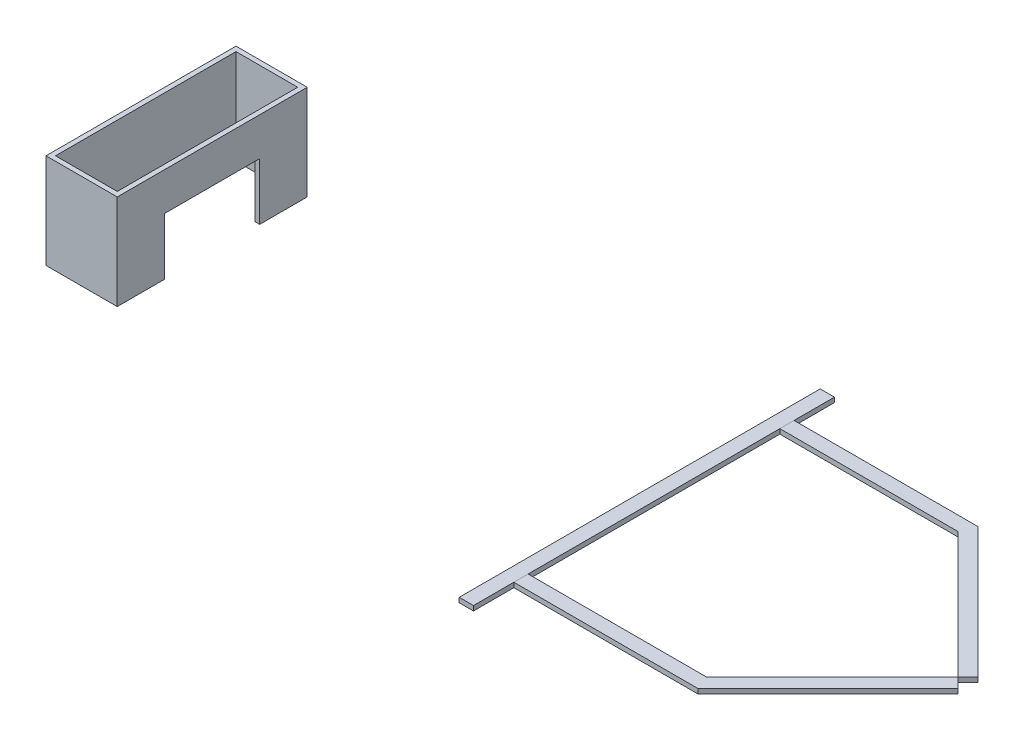
SolidWorks part; units mm, degrees
ref_plane "Front Plane" through (0, 0, 0) normal (0, 0, 1) x (1, 0, 0)
ref_plane "Top Plane" through (0, 0, 0) normal (0, 1, 0) x (1, 0, 0)
ref_plane "Right Plane" through (0, 0, 0) normal (1, 0, 0) x (0, 0, -1)
sketch "Sketch1" plane through (0, 0, 0) normal (0, 1, 0) x (1, 0, 0)
  line L6 (346.8244, -129.6488) -> (368.0376, -108.4356)
  line L16 (-292.9422, 135.3512) -> (81.8244, 135.3512)
  line L17 (81.8244, 135.3512) -> (346.8244, -129.6488)
  line L18 (-292.9422, 165.3512) -> (94.2508, 165.3512)
  line L19 (94.2508, 165.3512) -> (368.0376, -108.4356)
  line L20 (-292.9422, 165.3512) -> (-292.9422, 135.3512)
  line L21 (368.0376, -108.4356) -> (346.8244, -129.6488)
  line L22 (368.0376, -150.862) -> (346.8244, -129.6488)
  line L23 (-292.9422, -424.6488) -> (-292.9422, -394.6488)
  line L24 (94.2508, -424.6488) -> (368.0376, -150.862)
  line L25 (-292.9422, -424.6488) -> (94.2508, -424.6488)
  line L26 (81.8244, -394.6488) -> (346.8244, -129.6488)
  line L27 (-292.9422, -394.6488) -> (81.8244, -394.6488)
  point P1 (0, 0)
  point P2 (0, 0)
  dimension "D2" = 374.7666
  dimension "D3" = 374.7666
  dimension "D4" = 30
  dimension "D1" = 530
extrude "Boss-Extrude2" add sketch "Sketch1" along normal blind 10 contours L27 L23 L25 L24 L22 L26 | L21 L17 L16 L20 L18 L19
sketch "Sketch2" plane through (0, 0, 0) normal (0, 1, 0) x (1, 0, 0)
  line L0 (-292.9522, -129.6488) -> (346.8244, -129.6488) construction
  line L1 (-322.9522, 250.3512) -> (-292.9522, 250.3512)
  line L2 (-322.9522, 250.3512) -> (-322.9522, -509.6488)
  line L3 (-322.9522, -509.6488) -> (-292.9522, -509.6488)
  line L4 (-292.9522, 250.3512) -> (-292.9522, -509.6488)
  line L6 (-292.9422, 165.3512) -> (-292.9422, 135.3512) construction
  dimension "D1" = 760
  dimension "D2" = 30
  dimension "D3" = 0.01
extrude "Boss-Extrude9" add sketch "Sketch2" along normal blind 10 separate body contours L2 L1 L4 L3
sketch "Sketch3" plane through (0, 0, 0) normal (0, 1, 0) x (1, 0, 0)
  line L0 (-322.9522, 250.3512) -> (-322.9522, -509.6488) construction
  line L1 (-1222.9522, 70.3512) -> (-1372.9522, 70.3512)
  line L2 (-1222.9522, 70.3512) -> (-1222.9522, -329.6488)
  line L3 (-1222.9522, -329.6488) -> (-1372.9522, -329.6488)
  line L4 (-1372.9522, 70.3512) -> (-1372.9522, -329.6488)
  line L5 (-322.9522, -129.6488) -> (-1222.9522, -129.6488) construction
  dimension "D1" = 150
  dimension "D2" = 400
  dimension "D3" = 900
extrude "Boss-Extrude10" add sketch "Sketch3" along normal blind 200 separate body contours L2 L1 L4 L3
sketch "Sketch4" plane through (0, 0, 0) normal (0, 1, 0) x (1, 0, 0)
  line L0 (-1362.9522, -319.6488) -> (-1232.9522, -319.6488)
  line L1 (-1232.9522, -319.6488) -> (-1232.9522, 60.3512)
  line L2 (-1232.9522, 60.3512) -> (-1362.9522, 60.3512)
  line L3 (-1362.9522, 60.3512) -> (-1362.9522, -319.6488)
extrude "Cut-Extrude2" cut sketch "Sketch4" along normal blind 200
sketch "Sketch5" plane through (-1222.9522, 0, 0) normal (1, 0, 0) x (0, 0, -1)
  line L0 (-329.6488, 200) -> (-329.6488, 0) construction
  line L1 (-229.6488, 120) -> (-29.6488, 120)
  line L2 (-229.6488, 120) -> (-229.6488, 0)
  line L3 (-229.6488, 0) -> (-29.6488, 0)
  line L4 (-29.6488, 120) -> (-29.6488, 0)
  line L5 (70.3512, 0) -> (-329.6488, 0) construction
  dimension "D1" = 200
  dimension "D2" = 120
  dimension "D3" = 100
extrude "Cut-Extrude3" cut sketch "Sketch5" against normal blind 10
